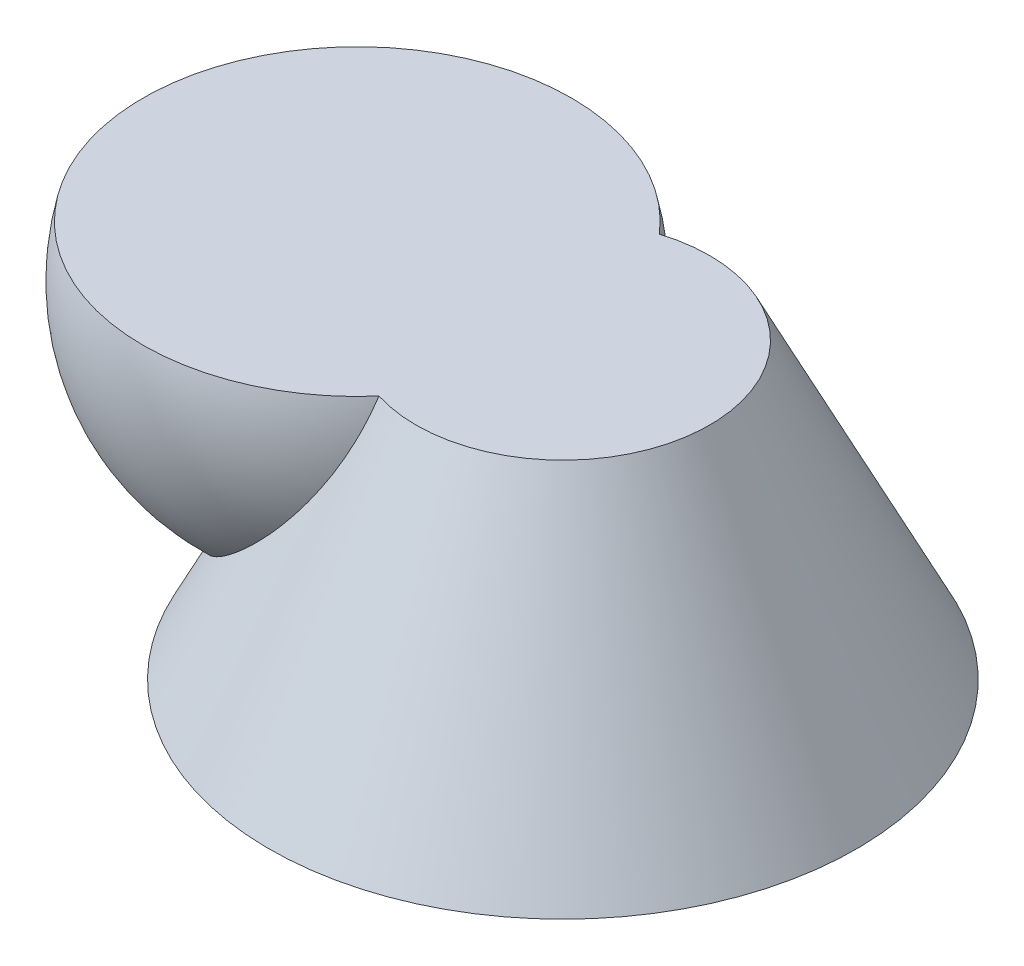
SolidWorks part; units mm, degrees
ref_plane "Front Plane" through (0, 0, 0) normal (0, 0, 1) x (1, 0, 0)
ref_plane "Top Plane" through (0, 0, 0) normal (0, 1, 0) x (1, 0, 0)
ref_plane "Right Plane" through (0, 0, 0) normal (1, 0, 0) x (0, 0, -1)
sketch "Sketch1" plane through (0, 0, 0) normal (0, 0, 1) x (1, 0, 0)
  line L0 (0, 3) -> (0, 63)
  arc A0 (0, 63) -> (0, 3) centre (0, 33) ccw
  dimension "D1" = 60
  dimension "D2" = 33
revolve "Revolve1" add sketch "Sketch1" angle 360 about L0
sketch "Sketch2" plane through (0, 0, 0) normal (0, 0, 1) x (1, 0, 0)
  line L0 (-12, 0) -> (28, 80)
  line L1 (28, 80) -> (28, 0)
  line L2 (28, 0) -> (-12, 0)
  dimension "D1" = 80
  dimension "D2" = 28
  dimension "D3" = 40
revolve "Revolve2" add sketch "Sketch2" angle 360 about L1
ref_plane "Cutting Plane" through (0, 40, 0) normal (0, 1, 0) x (1, 0, 0)
other "SurfaceCut1"
